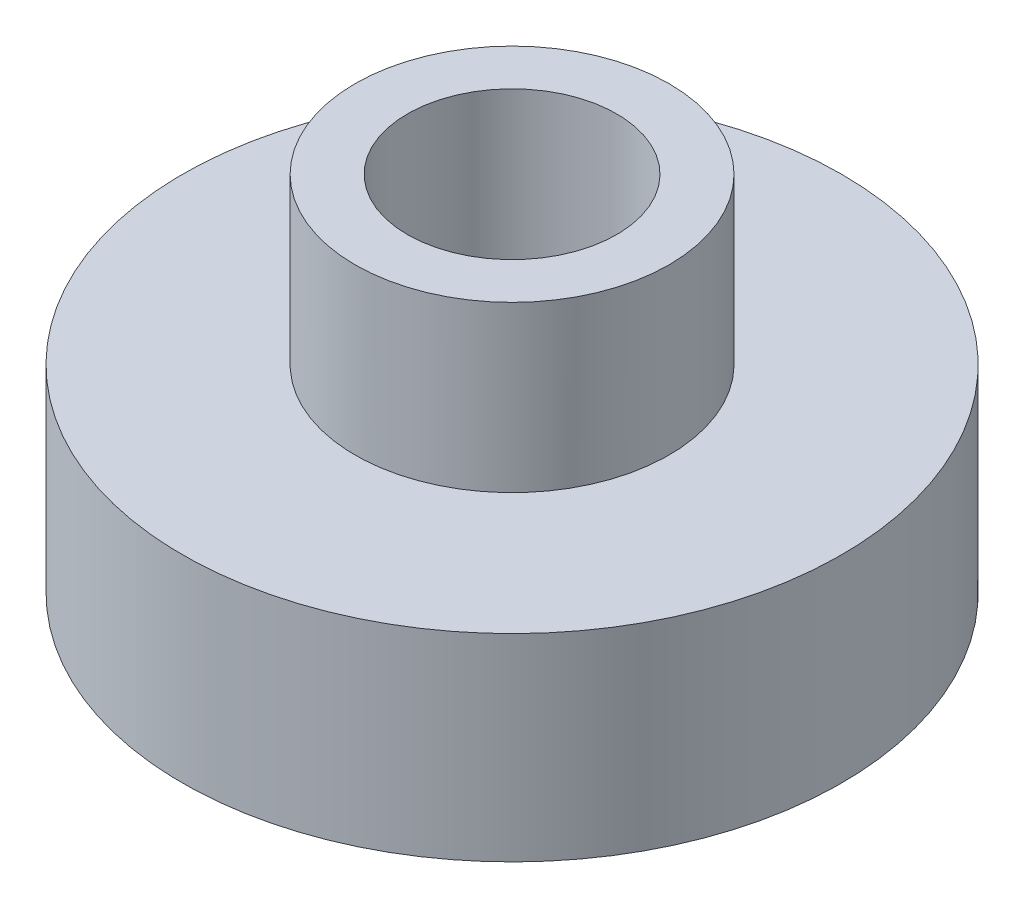
SolidWorks part; units mm, degrees
ref_plane "Front Plane" through (0, 0, 0) normal (0, 0, 1) x (1, 0, 0)
ref_plane "Top Plane" through (0, 0, 0) normal (0, 1, 0) x (1, 0, 0)
ref_plane "Right Plane" through (0, 0, 0) normal (1, 0, 0) x (0, 0, -1)
sketch "Sketch1" plane through (0, 0, 0) normal (0, 1, 0) x (1, 0, 0)
  circle A0 centre (0, 0) radius 20
  circle A1 centre (0, 0) radius 6.35
  circle A2 centre (0, 0) radius 9.525
  dimension "D1" = 40
  dimension "D2" = 12.7
  dimension "D3" = 19.05
extrude "Boss-Extrude1" add sketch "Sketch1" along normal blind 22 contours A2 A1
sketch "Sketch2" plane through (0, 0, 0) normal (0, -1, 0) x (1, 0, 0)
  circle A0 centre (0, 0) radius 20
  circle A1 centre (0, 0) radius 9.525
  dimension "D1" = 40
extrude "Boss-Extrude2" add sketch "Sketch2" against normal blind 12
